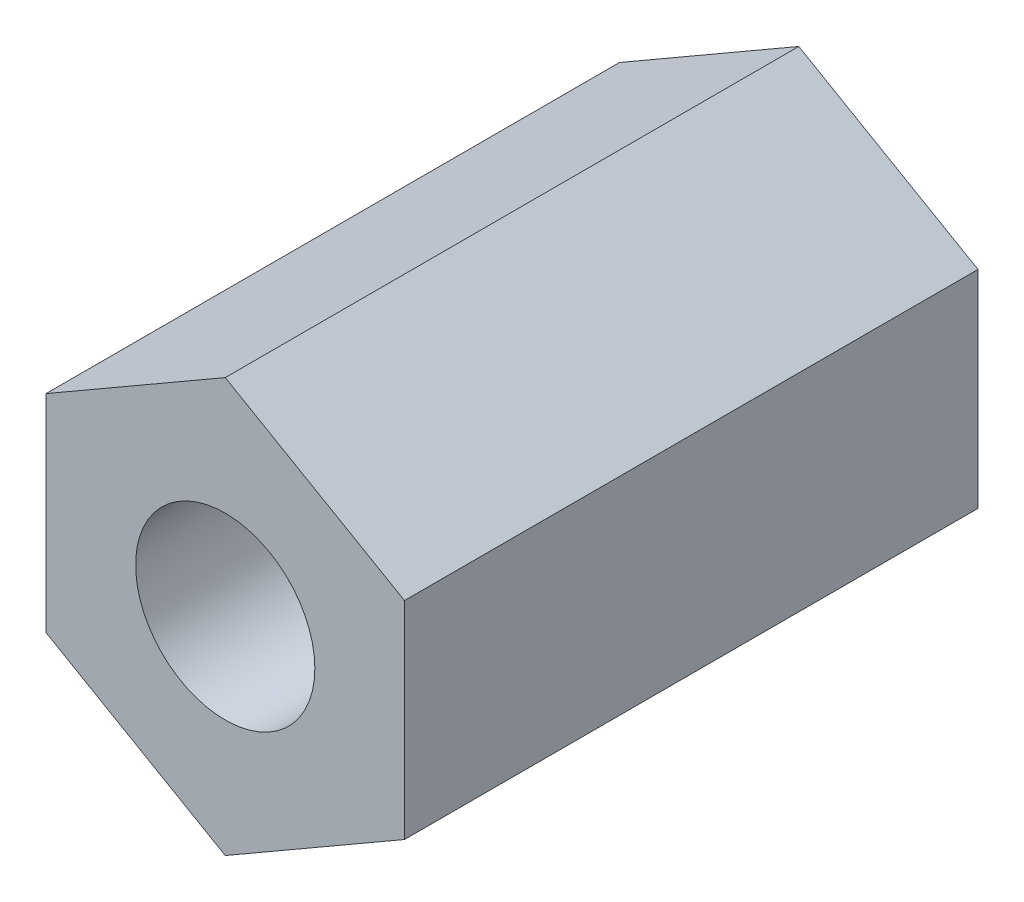
SolidWorks part; units mm, degrees
material "Bronze commercial, UNS C22000 (90-10 Bronze)"
ref_plane "Plan de face" through (0, 0, 0) normal (0, 0, 1) x (1, 0, 0)
ref_plane "Plan de dessus" through (0, 0, 0) normal (0, 1, 0) x (1, 0, 0)
ref_plane "Plan de droite" through (0, 0, 0) normal (1, 0, 0) x (0, 0, -1)
sketch "Esquisse1" plane through (0, 0, 0) normal (0, 0, 1) x (1, 0, 0)
  line L1 (2.5, -1.4434) -> (2.5, 1.4434)
  line L2 (2.5, 1.4434) -> (0, 2.8868)
  line L3 (0, 2.8868) -> (-2.5, 1.4434)
  line L4 (-2.5, 1.4434) -> (-2.5, -1.4434)
  line L5 (-2.5, -1.4434) -> (0, -2.8868)
  line L6 (0, -2.8868) -> (2.5, -1.4434)
  circle A0 centre (0, 0) radius 2.5 construction
  dimension "D1" = 5
extrude "Boss.-Extru.1" add sketch "Esquisse1" along normal blind 8
hole_wizard "Trou pour taraudage pour trou taraudé M31" positions "Esquisse3" profile "Esquisse2" hole size "M3" standard "ISO" end condition up to next
sketch "Esquisse3" plane through (0, 0, 8) normal (0, 0, 1) x (1, 0, 0)
  point P0 (0, 0)
sketch "Esquisse2" plane through (0, 0, 8) normal (1, 0, 0) x (0, -1, 0)
  line L0 (0, 0) -> (0, 8)
  line L1 (0, 8) -> (1.25, 8)
  line L2 (1.25, 8) -> (1.25, 0)
  line L5 (1.25, 0) -> (0, 0)
  line L11 (0, -6.35) -> (0, 107.95) construction
  dimension "Diamètre du perçage jusqu'au prochain" = 2.5
  dimension "Profondeur du perçage jusqu'au prochain" = 8
